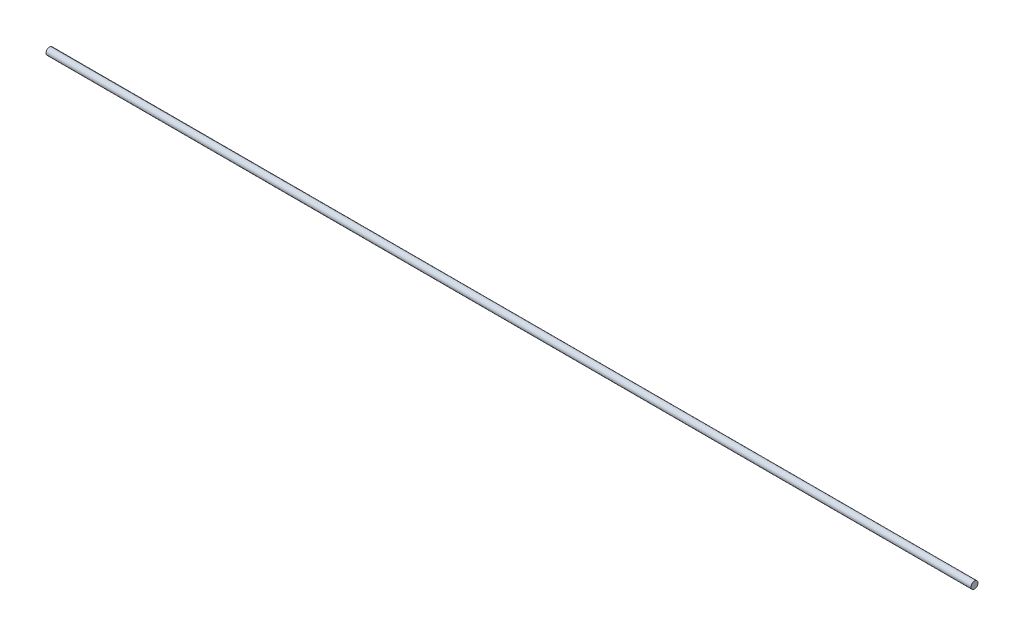
SolidWorks part; units mm, degrees
ref_plane "Front Plane" through (0, 0, 0) normal (0, 0, 1) x (1, 0, 0)
ref_plane "Top Plane" through (0, 0, 0) normal (0, 1, 0) x (1, 0, 0)
ref_plane "Right Plane" through (0, 0, 0) normal (1, 0, 0) x (0, 0, -1)
sketch "Sketch1" plane through (0, 0, 0) normal (1, 0, 0) x (0, 0, -1)
  circle A0 centre (0, 0) radius 3.175
  dimension "D1" = 6.35
extrude "Boss-Extrude1" add sketch "Sketch1" along normal blind 838.2
